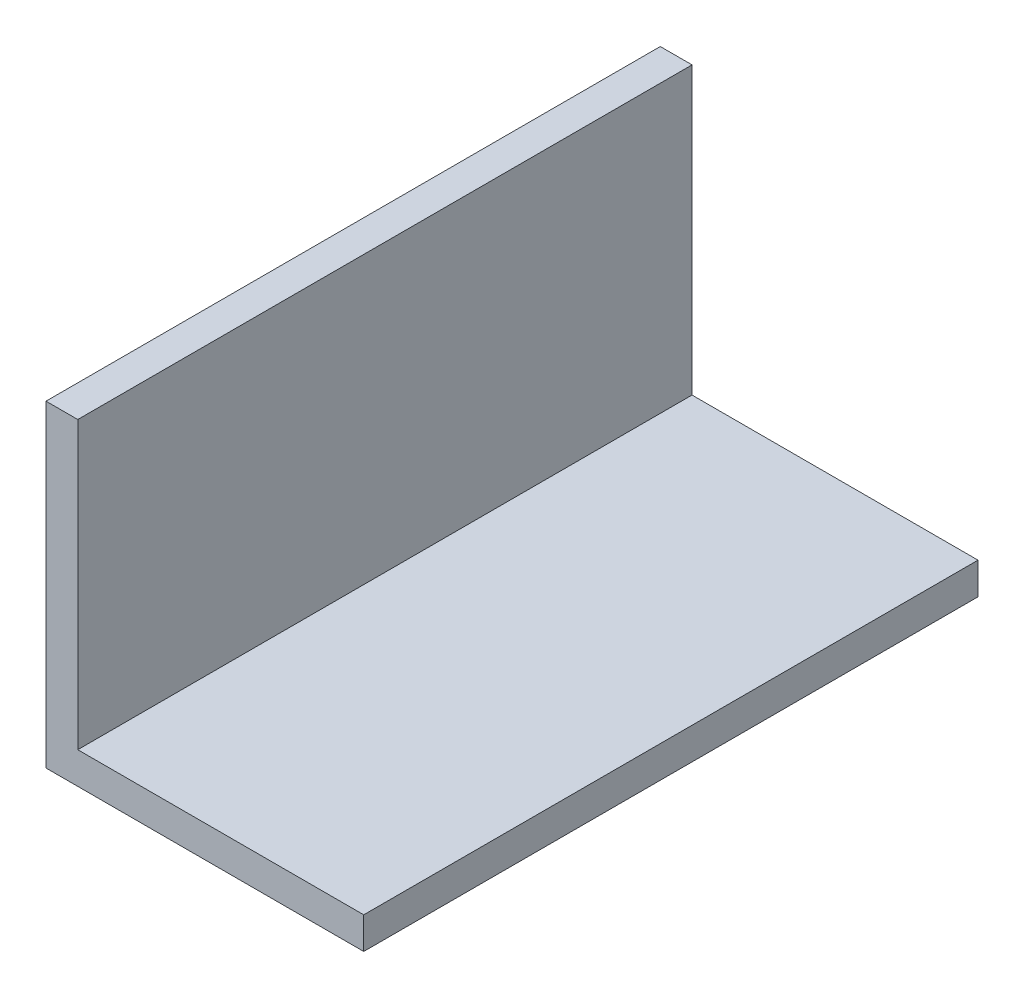
SolidWorks part; units mm, degrees
ref_plane "Спереди" through (0, 0, 0) normal (0, 0, 1) x (1, 0, 0)
ref_plane "Сверху" through (0, 0, 0) normal (0, 1, 0) x (1, 0, 0)
ref_plane "Справа" through (0, 0, 0) normal (1, 0, 0) x (0, 0, -1)
sketch "Эскиз1" plane through (0, 0, 0) normal (0, 0, 1) x (1, 0, 0)
  line L0 (0, 30) -> (0, 0)
  line L1 (0, 0) -> (30, 0)
  line L2 (0, 30) -> (3, 30)
  line L3 (3, 30) -> (3, 3)
  line L4 (3, 3) -> (30, 3)
  line L5 (30, 3) -> (30, 0)
extrude "Бобышка-Вытянуть1" add sketch "Эскиз1" along normal blind 58
